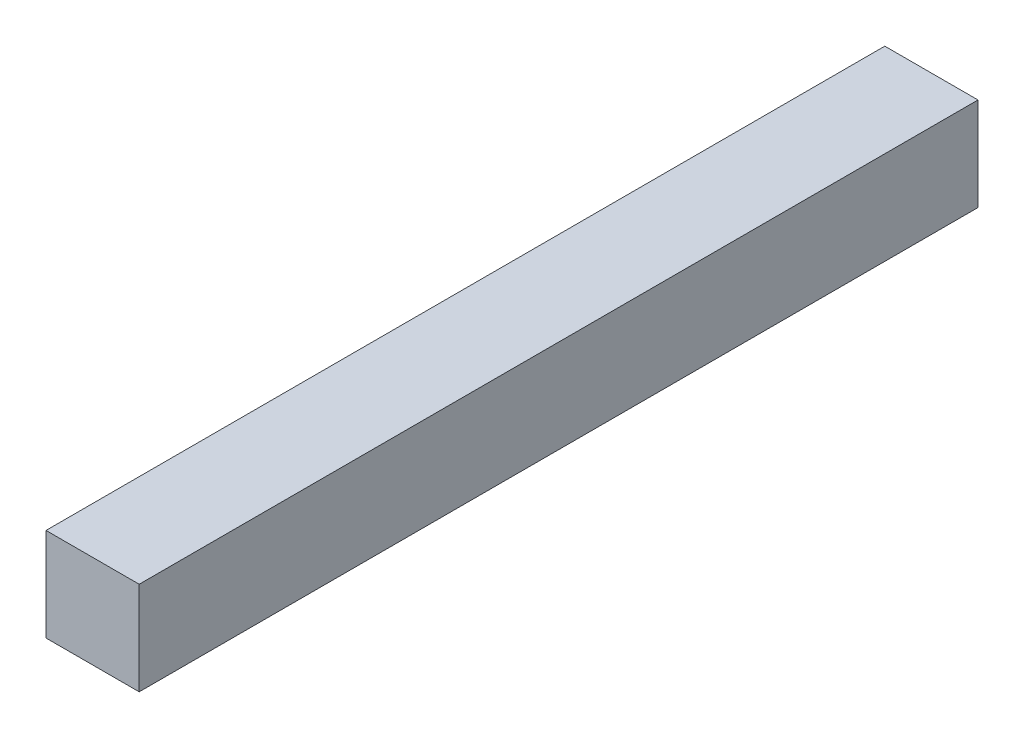
SolidWorks part; units mm, degrees
ref_plane "Front Plane" through (0, 0, 0) normal (0, 0, 1) x (1, 0, 0)
ref_plane "Top Plane" through (0, 0, 0) normal (0, 1, 0) x (1, 0, 0)
ref_plane "Right Plane" through (0, 0, 0) normal (1, 0, 0) x (0, 0, -1)
sketch "Sketch1" plane through (0, 0, 0) normal (0, 0, 1) x (1, 0, 0)
  line L1 (-10, 10) -> (10, 10)
  line L2 (-10, 10) -> (-10, -10)
  line L3 (-10, -10) -> (10, -10)
  line L4 (10, 10) -> (10, -10)
  line L5 (-10, 10) -> (10, -10) construction
  line L6 (-10, -10) -> (10, 10) construction
  point P0 (0, 0)
  dimension "D1" = 20
  dimension "D2" = 20
extrude "Boss-Extrude1" add sketch "Sketch1" along normal blind 180
